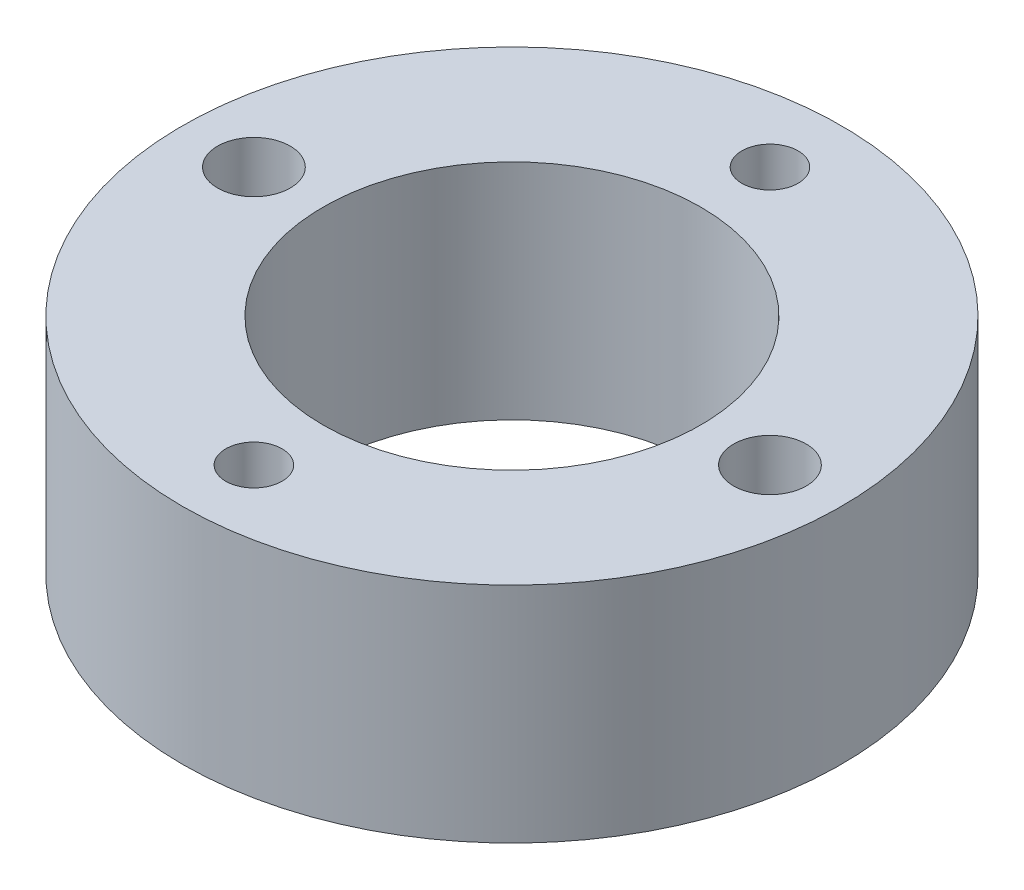
SolidWorks part; units mm, degrees
ref_plane "Front Plane" through (0, 0, 0) normal (0, 0, 1) x (1, 0, 0)
ref_plane "Top Plane" through (0, 0, 0) normal (0, 1, 0) x (1, 0, 0)
ref_plane "Right Plane" through (0, 0, 0) normal (1, 0, 0) x (0, 0, -1)
sketch "Sketch1" plane through (0, 0, 0) normal (0, 1, 0) x (1, 0, 0)
  circle A0 centre (0, 0) radius 8.05
  circle A1 centre (0, 0) radius 14.05
  circle A2 centre (0, 0) radius 11 construction
  circle A3 centre (11, 0) radius 1.55
  circle A4 centre (-11, 0) radius 1.55
  circle A5 centre (0, 11) radius 1.2
  circle A6 centre (0, -11) radius 1.2
  dimension "D1" = 16.1
  dimension "D2" = 6
  dimension "D3" = 22
  dimension "D4" = 3.1
  dimension "D5" = 2.4
extrude "Boss-Extrude1" add sketch "Sketch1" along normal blind 9.525
